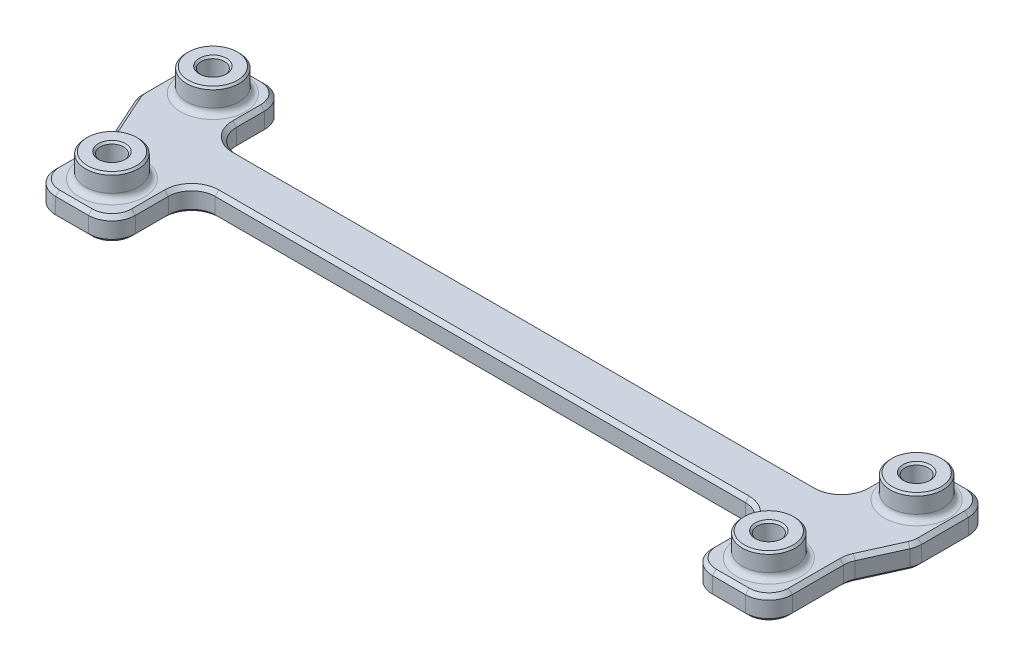
SolidWorks part; units mm, degrees
ref_plane "Front" through (0, 0, 0) normal (0, 0, 1) x (1, 0, 0)
ref_plane "Top" through (0, 0, 0) normal (0, 1, 0) x (1, 0, 0)
ref_plane "Right" through (0, 0, 0) normal (1, 0, 0) x (0, 0, -1)
sketch "Sketch2" plane through (0, 0, 0) normal (0, 1, 0) x (1, 0, 0)
  line L0 (-47.1551, 13.3477) -> (-45.7136, 13.3477) construction
  line L5 (-52.7113, 3.175) -> (-42.5386, 3.175) construction
  line L6 (-52.7113, 3.175) -> (-52.7113, 13.3477) construction
  line L7 (-52.7113, 13.3477) -> (-42.5386, 13.3477) construction
  line L8 (-42.5386, 3.175) -> (-42.5386, 13.3477) construction
  line L9 (-52.7113, 3.175) -> (-42.5386, 13.3477) construction
  line L10 (-52.7113, 13.3477) -> (-42.5386, 3.175) construction
  line L11 (-42.5386, 10.1727) -> (-42.5386, 8.7313) construction
  line L12 (45.7137, 13.3477) -> (47.1551, 13.3477) construction
  line L13 (52.7114, 3.175) -> (42.5387, 3.175) construction
  line L14 (52.7114, 3.175) -> (52.7114, 13.3477) construction
  line L15 (52.7114, 13.3477) -> (42.5387, 13.3477) construction
  line L16 (42.5387, 3.175) -> (42.5387, 13.3477) construction
  line L17 (52.7114, 3.175) -> (42.5387, 13.3477) construction
  line L18 (52.7114, 13.3477) -> (42.5387, 3.175) construction
  line L19 (42.5387, 8.7313) -> (42.5387, 10.1727) construction
  line L20 (44.2913, -13.97) -> (42.2275, -13.97) construction
  line L21 (49.8475, -3.175) -> (39.0525, -3.175) construction
  line L22 (49.8475, -3.175) -> (49.8475, -13.97) construction
  line L23 (49.8475, -13.97) -> (39.0525, -13.97) construction
  line L24 (39.0525, -3.175) -> (39.0525, -13.97) construction
  line L25 (49.8475, -3.175) -> (39.0525, -13.97) construction
  line L26 (49.8475, -13.97) -> (39.0525, -3.175) construction
  line L27 (39.0525, -10.795) -> (39.0525, -8.7312) construction
  line L28 (-39.0525, -8.7312) -> (-39.0525, -10.795) construction
  line L29 (-49.8475, -3.175) -> (-39.0525, -3.175) construction
  line L30 (-49.8475, -3.175) -> (-49.8475, -13.97) construction
  line L31 (-49.8475, -13.97) -> (-39.0525, -13.97) construction
  line L32 (-39.0525, -3.175) -> (-39.0525, -13.97) construction
  line L33 (-49.8475, -3.175) -> (-39.0525, -13.97) construction
  line L34 (-49.8475, -13.97) -> (-39.0525, -3.175) construction
  line L35 (-42.2275, -13.97) -> (-44.2912, -13.97) construction
  line L36 (-39.0525, -13.97) -> (-39.0525, -3.175)
  line L37 (-39.0525, -3.175) -> (39.0525, -3.175)
  line L38 (39.0525, -3.175) -> (39.0525, -13.97)
  line L39 (39.0525, -13.97) -> (49.8475, -13.97)
  line L40 (49.8475, -13.97) -> (49.8475, -3.175)
  line L41 (49.8475, -3.175) -> (52.7114, 3.175)
  line L42 (52.7114, 3.175) -> (52.7114, 13.3477)
  line L43 (52.7114, 13.3477) -> (42.5387, 13.3477)
  line L44 (42.5387, 13.3477) -> (42.5387, 3.175)
  line L45 (42.5387, 3.175) -> (-42.5386, 3.175)
  line L46 (-42.5386, 3.175) -> (-42.5386, 13.3477)
  line L47 (-42.5386, 13.3477) -> (-52.7113, 13.3477)
  line L48 (-52.7113, 13.3477) -> (-52.7113, 3.175)
  line L49 (-52.7113, 3.175) -> (-49.8475, -3.175)
  line L50 (-49.8475, -3.175) -> (-49.8475, -13.97)
  line L51 (-49.8475, -13.97) -> (-39.0525, -13.97)
  point P0 (-47.625, 8.2614)
  point P11 (47.625, 8.2614)
  point P21 (44.45, -8.5725)
  point P31 (-44.45, -8.5725)
extrude "Boss-Extrude2" add sketch "Sketch2" along normal blind 3.175
sketch "Sketch3" plane through (0, 3.175, 0) normal (0, 1, 0) x (1, 0, 0)
  line L0 (-42.5386, 13.3477) -> (-52.7113, 13.3477) construction
  line L1 (-42.5386, 3.175) -> (-42.5386, 13.3477) construction
  line L2 (-52.7113, 13.3477) -> (-52.7113, 3.175) construction
  line L3 (-39.0525, -13.97) -> (-39.0525, -3.175) construction
  line L4 (-49.8475, -13.97) -> (-39.0525, -13.97) construction
  line L5 (-49.8475, -3.175) -> (-49.8475, -13.97) construction
  line L6 (52.7114, 13.3477) -> (42.5387, 13.3477) construction
  line L7 (52.7114, 3.175) -> (52.7114, 13.3477) construction
  line L8 (42.5387, 13.3477) -> (42.5387, 3.175) construction
  line L9 (49.8475, -13.97) -> (49.8475, -3.175) construction
  line L12 (39.0525, -3.175) -> (39.0525, -13.97) construction
  line L13 (39.0525, -13.97) -> (49.8475, -13.97) construction
  circle A0 centre (-47.625, 8.2614) radius 5.0864 construction
  circle A1 centre (-44.45, -8.5725) radius 5.3975 construction
  circle A2 centre (47.625, 8.2614) radius 5.0864 construction
  circle A3 centre (44.45, -8.5725) radius 5.3975 construction
  circle A4 centre (-47.625, 8.2614) radius 3.5719
  circle A5 centre (-44.45, -8.5725) radius 3.5719
  circle A6 centre (44.45, -8.5725) radius 3.5719
  circle A7 centre (47.625, 8.2614) radius 3.5719
  dimension "D1" = 7.1437
extrude "Boss-Extrude3" add sketch "Sketch3" along normal blind 3.175 contours A4
sketch "Sketch4" plane through (0, 0, 0) normal (0, -1, 0) x (1, 0, 0)
  circle A0 centre (-44.45, 8.5725) radius 1.5875
  circle A1 centre (-47.625, -8.2614) radius 1.5875
  circle A2 centre (47.625, -8.2614) radius 1.5875
  circle A3 centre (44.45, 8.5725) radius 1.5875
  circle A4 centre (44.45, 8.5725) radius 3.5719 construction
  circle A5 centre (47.625, -8.2614) radius 3.5719 construction
  circle A6 centre (-47.625, -8.2614) radius 3.5719 construction
  circle A7 centre (-44.45, 8.5725) radius 3.5719 construction
  dimension "D1" = 3.175
extrude "Cut-Extrude1" cut sketch "Sketch4" against normal up to next
fillet "Fillet1" radius 3.175 16 edges at (-42.5386, 1.5875, -13.3477) (-42.5386, 1.5875, -3.175) (42.5387, 1.5875, -3.175) (42.5387, 1.5875, -13.3477) (52.7114, 1.5875, -13.3477) (52.7114, 1.5875, -3.175) (49.8475, 1.5875, 3.175) (49.8475, 1.5875, 13.97) (39.0525, 1.5875, 13.97) (39.0525, 1.5875, 3.175) (-39.0525, 1.5875, 13.97) (-49.8475, 1.5875, 13.97) (-49.8475, 1.5875, 3.175) (-52.7113, 1.5875, -3.175) (-52.7113, 1.5875, -13.3477) (-39.0525, 1.5875, 3.175)
fillet "Fillet2" radius 0.7937 4 edges at (44.45, 3.175, 12.1444) (47.625, 3.175, -4.6895) (-47.625, 3.175, -4.6895) (-44.45, 3.175, 12.1444)
chamfer "Chamfer1" distance 0.508 angle 45 64 edges at (0, 3.175, -3.175) (-41.6087, 3.175, -4.1049) (41.6087, 3.175, -4.1049) (-42.5386, 3.175, -8.2614) (42.5387, 3.175, -8.2614) (-43.4686, 3.175, -12.4178) (43.4686, 3.175, -12.4178) (-47.625, 3.175, -13.3477) (47.625, 3.175, -13.3477) (-51.7814, 3.175, -12.4178) (51.7814, 3.175, -12.4178) (-52.7113, 3.175, -7.0153) (52.7114, 3.175, -7.0153) (-52.6404, 3.175, -3.1903) (52.6404, 3.175, -3.1903) (-51.2794, 3.175, 0) (51.2794, 3.175, 0) (-49.9185, 3.175, 3.1903) (49.9185, 3.175, 3.1903) (-49.8475, 3.175, 7.3264) (49.8475, 3.175, 7.3264) (-48.9176, 3.175, 13.0401) (48.9176, 3.175, 13.0401) (-44.45, 3.175, 13.97) (44.45, 3.175, 13.97) (-39.9824, 3.175, 13.0401) (39.9824, 3.175, 13.0401) (-39.0525, 3.175, 8.5725) (39.0525, 3.175, 8.5725) (-38.1226, 3.175, 4.1049) (38.1226, 3.175, 4.1049) (0, 3.175, 3.175) (0, 0, -3.175) (-41.6087, 0, -4.1049) (41.6087, 0, -4.1049) (-42.5386, 0, -8.2614) (42.5387, 0, -8.2614) (-43.4686, 0, -12.4178) (43.4686, 0, -12.4178) (-47.625, 0, -13.3477) (47.625, 0, -13.3477) (-51.7814, 0, -12.4178) (51.7814, 0, -12.4178) (-52.7113, 0, -7.0153) (52.7114, 0, -7.0153) (-52.6404, 0, -3.1903) (52.6404, 0, -3.1903) (-51.2794, 0, 0) (51.2794, 0, 0) (-49.9185, 0, 3.1903) (49.9185, 0, 3.1903) (-49.8475, 0, 7.3264) (49.8475, 0, 7.3264) (-48.9176, 0, 13.0401) (48.9176, 0, 13.0401) (-44.45, 0, 13.97) (44.45, 0, 13.97) (-39.9824, 0, 13.0401) (39.9824, 0, 13.0401) (-39.0525, 0, 8.5725) (39.0525, 0, 8.5725) (-38.1226, 0, 4.1049) (38.1226, 0, 4.1049) (0, 0, 3.175)
chamfer "Chamfer2" distance 0.254 angle 45 12 edges at (44.45, 0, 6.985) (44.45, 6.35, 10.16) (47.625, 0, -9.8489) (47.625, 6.35, -6.6739) (-47.625, 0, -9.8489) (-47.625, 6.35, -6.6739) (-44.45, 0, 6.985) (-44.45, 6.35, 10.16) (44.45, 6.35, 12.1444) (47.625, 6.35, -4.6895) (-47.625, 6.35, -4.6895) (-44.45, 6.35, 12.1444)
